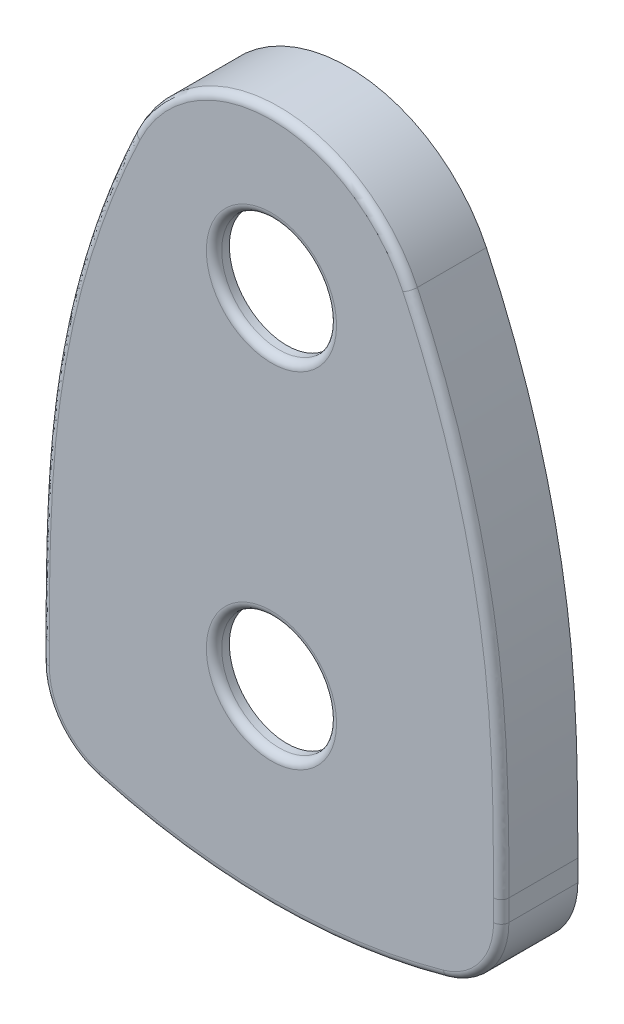
SolidWorks part; units mm, degrees
ref_plane "前视基准面" through (0, 0, 0) normal (0, 0, 1) x (1, 0, 0)
ref_plane "上视基准面" through (0, 0, 0) normal (0, 1, 0) x (1, 0, 0)
ref_plane "右视基准面" through (0, 0, 0) normal (1, 0, 0) x (0, 0, -1)
sketch "草图1" plane through (0, 0, 0) normal (0, 0, 1) x (1, 0, 0)
  line L0 (0, 0) -> (0, -70) construction
  line L2 (-30, -54.4602) -> (-30, -64.4602)
  line L3 (30, -54.4602) -> (30, -64.4602)
  circle A0 centre (0, 0) radius 20
  arc A1 (-30, -64.4602) -> (30, -64.4602) centre (0, 14) ccw
  spline S0 degree 3 poles (-18.0595, 8.5939) (-23.9482, -3.7808) (-29.6965, -24.3413) (-30, -45.9531) (-30, -54.4602) knots 0 0 0 0 0.608662 1 1 1 1
  spline S1 degree 3 poles (18.0595, 8.5939) (23.4238, -2.6788) (29.8651, -24.4322) (30, -46.2917) (30, -54.4602) knots 0 0 0 0 0.608662 1 1 1 1
  point P12 (0, 0)
  point P13 (0, 0)
  point P14 (-18.0595, 8.5939)
  point P15 (28.9286, -29.1991)
  point P17 (0, 0)
  point P18 (0, 0)
  dimension "D1" = 40
  dimension "D2" = 90
  dimension "D5" = 84
  dimension "D3" = 60
  dimension "D4" = 10
extrude "凸台-拉伸1" add sketch "草图1" along normal blind 10
fillet "圆角1" radius 10 2 edges at (-30, -64.4602, 5) (30, -64.4602, 5)
shell "抽壳1" thickness 2
sketch "草图2" plane through (0, 0, 10) normal (0, 0, 1) x (1, 0, 0)
  circle A0 centre (0, 0) radius 7.5
  circle A1 centre (0, -45) radius 7.5
  point P5 (0, 0)
  dimension "D1" = 15
  dimension "D2" = 45
extrude "切除-拉伸1" cut sketch "草图2" against normal blind 10
fillet "圆角2" radius 1 10 edges at (0, 20, 10) (30, -55.8531, 10) (27.9695, -63.2865, 10) (0, -70, 10) (-27.9695, -63.2865, 10) (-30, -55.8531, 10) (7.5, -45, 10) (7.5, 0, 10)
